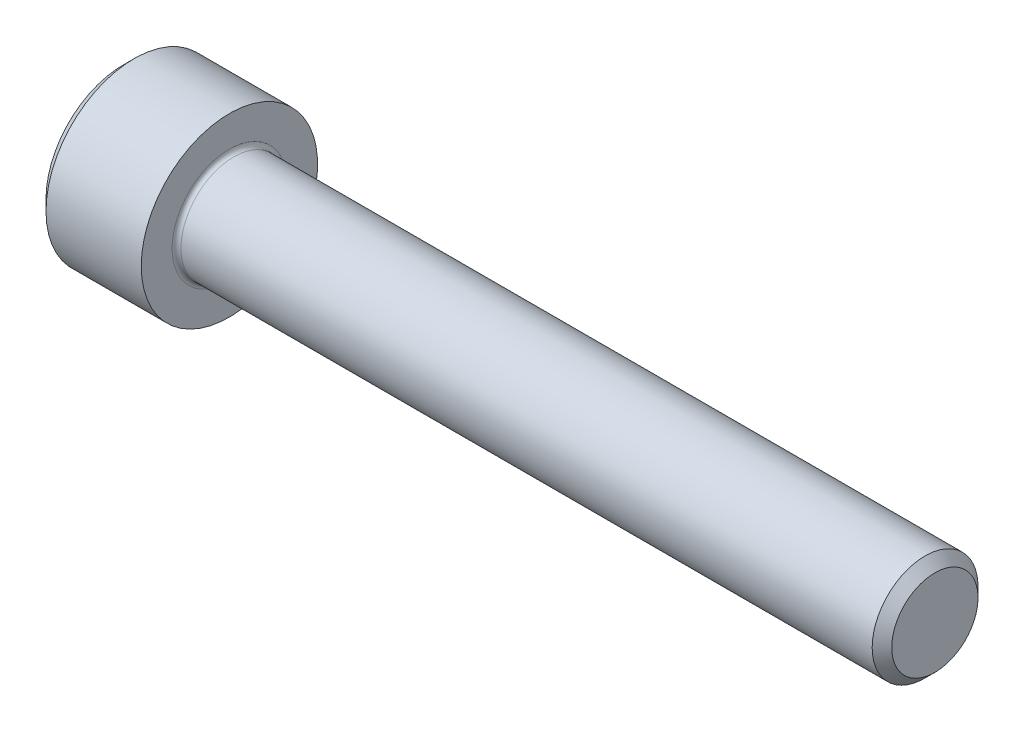
SolidWorks part; units mm, degrees
revolve "Base-Revolve" add sketch "BodySke"
sketch "BodySke" plane through (0, 0, 0) normal (0, 0, 1) x (1, 0, 0)
  line L0 (0, 0) -> (0, 4.4)
  line L1 (0.6, 5) -> (6, 5)
  line L2 (6, 5) -> (6, 3)
  line L3 (6, 3) -> (45.4455, 3)
  line L4 (46, 2.4455) -> (46, 0)
  line L5 (46, 0) -> (0, 0)
  line L6 (-31.75, 0) -> (127, 0) construction
  line L7 (0, 4.4) -> (0.6, 5)
  line L8 (46, 2.4455) -> (45.4455, 3)
  line L9 (0, -4.4) -> (0.6, -5) construction
  line L10 (46, -2.4455) -> (45.4455, -3) construction
  line L11 (7, 9.525) -> (7, 3.175) construction
  line L12 (22, 9.525) -> (22, 3.175) construction
  line L13 (-4, 9.525) -> (-4, 3.175) construction
  dimension "Diameter" = 6
  dimension "Head_ht" = 6
  dimension "Length" = 40
  dimension "Body_ch_ang" = 45
  dimension "Head_dia" = 10
  dimension "Head_ch_ang" = 45
  dimension "Minor_dia" = 4.891
  dimension "Advance" = 1
  dimension "Thread_nom" = 24
  dimension "Thread_length" = 50
  dimension "Head_ch_ht" = 0.6
cosmetic thread "ThreadCosmetic" [suppressed]
fillet "Fillet1" radius 0.25 1 edges at (6, 0, 3)
ref_plane "Plane1" through (0, 0, 0) normal (0, 0, 1) x (1, 0, 0)
ref_plane "Plane2" through (0, 0, 0) normal (0, 1, 0) x (1, 0, 0)
ref_plane "Plane3" through (0, 0, 0) normal (1, 0, 0) x (0, 0, -1)
sketch "Sketch2" plane through (0, 0, 0) normal (0, 0, 1) x (1, 0, 0)
  line L0 (0, 2.542) -> (3, 2.542)
  line L1 (3, 2.542) -> (4.4676, 0)
  line L2 (-31.75, 0) -> (127, 0) construction
  line L3 (4.4676, 0) -> (0, 0)
  line L4 (0, 0) -> (0, 2.542)
  line L5 (0, 4.4) -> (0, -4.4) construction
  line L6 (0, 0) -> (47.625, 0) construction
  line L7 (6, -5) -> (6, 5) construction
  dimension "D2" = 60
revolve "Hex-PreBroach" cut sketch "Sketch2" angle 360 about L6
sketch "Sketch3" plane through (0, 0, 0) normal (-1, 0, 0) x (0, 0.5, 0.866)
  line L0 (1.4676, 2.542) -> (-1.4676, 2.542)
  line L1 (-1.4676, 2.542) -> (-2.9352, 0)
  line L2 (1.4676, 2.542) -> (2.9352, 0)
  line L3 (1.4676, -2.542) -> (2.9352, 0)
  line L4 (1.4676, -2.542) -> (-1.4676, -2.542)
  line L5 (-1.4676, -2.542) -> (-2.9352, 0)
extrude "Hex" cut sketch "Sketch3" against normal blind 3
sketch "Sketch4" plane through (0, 0, 0) normal (-1, 0, 0) x (0, 0, 1)
  line L0 (0, 0) -> (2.8067, 0)
  line L1 (0, 0) -> (6.1484, 3.5498) construction
  line L2 (0, 0) -> (1.4033, 2.4307)
  line L3 (2.3336, 0.614) -> (2.6851, 0.817)
  line L4 (1.6986, 1.7139) -> (2.0501, 1.9169)
  arc A0 (2.3336, 0.614) -> (1.6986, 1.7139) centre (0, 0) ccw
  arc A1 (2.8067, 0) -> (2.6851, 0.817) centre (0, 0) ccw
  arc A2 (1.4033, 2.4307) -> (2.0501, 1.9169) centre (0, 0) cw
  dimension "D1" = 30
  dimension "D2" = 60
extrude "Spline" [suppressed] cut sketch "Sketch4" against normal blind 3
pattern_circular "CirPattern1" [suppressed] count 6 every 60
sketch "Sketch5" plane through (0, 0, 0) normal (0, 0, 1) x (1, 0, 0)
  line L0 (-31.75, 0) -> (127, 0) construction
  line L2 (0, 4.4) -> (0, -4.4) construction
  circle A0 centre (2.3, 0) radius 0.675
  dimension "Drilled_hole_dia" = 1.35
  dimension "Drilled_hole_loc" = 2.3
extrude "Hole" [suppressed] cut sketch "Sketch5" against normal through all and the other way through all
pattern_circular "Drilled-4" [suppressed] count 2 every 60
pattern_circular "Drilled-6" [suppressed] count 3 every 60
sketch "ThdSchSke" plane through (0, 0, 0) normal (0, 0, 1) x (1, 0, 0)
  line L0 (22, -2.4455) -> (21.6117, -3)
  line L1 (22, -2.4455) -> (22.3883, -3)
  line L2 (22.3883, -3) -> (22.3883, -3.75)
  line L3 (-3.175, 0) -> (5.1513, 0) construction
  line L5 (22.3883, -3.75) -> (21.6117, -3.75)
  line L6 (21.6117, -3.75) -> (21.6117, -3)
  line L7 (0, 4.4) -> (0, -4.4) construction
revolve "ThreadSchematic" [suppressed] cut sketch "ThdSchSke" angle 360 about L3
pattern_linear "ThdSchPat" [suppressed]
equation "\"D2@Sketch3\" = \"Hex_size@Sketch3\" / 2"
equation "\"D1@Sketch3\" = \"Hex_size@Sketch3\" / 2"
equation "\"D1@Sketch2\" = \"Hex_size@Sketch3\" / 2"
equation "\"D3@Sketch4\" = \"Spline_p_dim@Sketch4\" / 2"
equation "\"Thread_minor@ThreadCosmetic\"  =  \"Minor_dia@BodySke\""
equation "\"D2@CirPattern1\" = 360 / \"Num_teeth@CirPattern1\""
equation "\"Wall_thickness@Sketch2\" = \"Head_ht@BodySke\" - \"Key_eng@Hex\""
equation "\"Thread_length@ThreadCosmetic\" = ((sgn( (\"Length@BodySke\" - \"Advance@BodySke\" ) - \"Thread_nom@BodySke\" )-1)*( (\"Length@BodySke\" - \"Advance@BodySke\" ) - \"Thread_nom@BodySke\" ))/-2+ \"Thread_nom@BodySke\""
equation "\"Thread_minor@ThdSchSke\" = \"Minor_dia@BodySke\""
equation "\"Diameter@ThdSchSke\" = \"Diameter@BodySke\""
equation "\"Overcut@ThdSchSke\" = \"Diameter@BodySke\" * 1.25"
equation "\"Start@ThdSchSke\" = \"Head_ht@BodySke\" + \"Length@BodySke\" - \"Thread_length@ThreadCosmetic\"  '---Non-countersunk---"
equation "\"Num_threads@ThdSchPat\" = int( \"Thread_length@ThreadCosmetic\" / \"Advance@BodySke\" + 0.999 )  + 1"
equation "\"Advance@ThdSchPat\" = \"Thread_length@ThreadCosmetic\" /  (\"Num_threads@ThdSchPat\" - 1) 'relax it"
equation "\"Num_threads@ThdSchPat\" = \"Num_threads@ThdSchPat\" - sgn( \"Num_threads@ThdSchPat\" - 1) '---chamfered tips only---"
